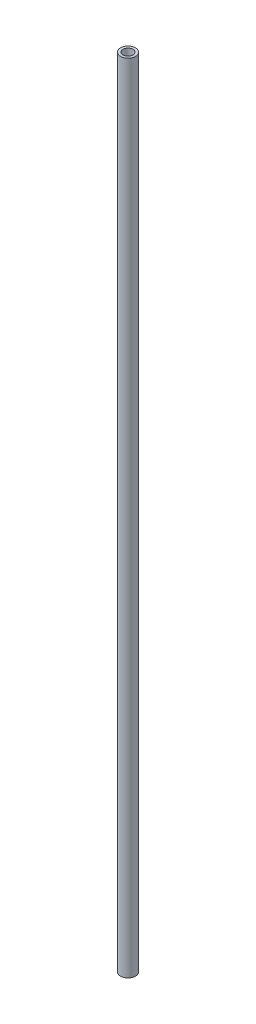
SolidWorks part; units mm, degrees
ref_plane "Front Plane" through (0, 0, 0) normal (0, 0, 1) x (1, 0, 0)
ref_plane "Top Plane" through (0, 0, 0) normal (0, 1, 0) x (1, 0, 0)
ref_plane "Right Plane" through (0, 0, 0) normal (1, 0, 0) x (0, 0, -1)
sketch "Sketch1" plane through (0, 0, 0) normal (0, 1, 0) x (1, 0, 0)
  circle A0 centre (0, 0) radius 9.525
  circle A1 centre (0, 0) radius 6.35
  dimension "D1" = 19.05
  dimension "D2" = 3.175
extrude "Boss-Extrude1" add sketch "Sketch1" along normal blind 1016
